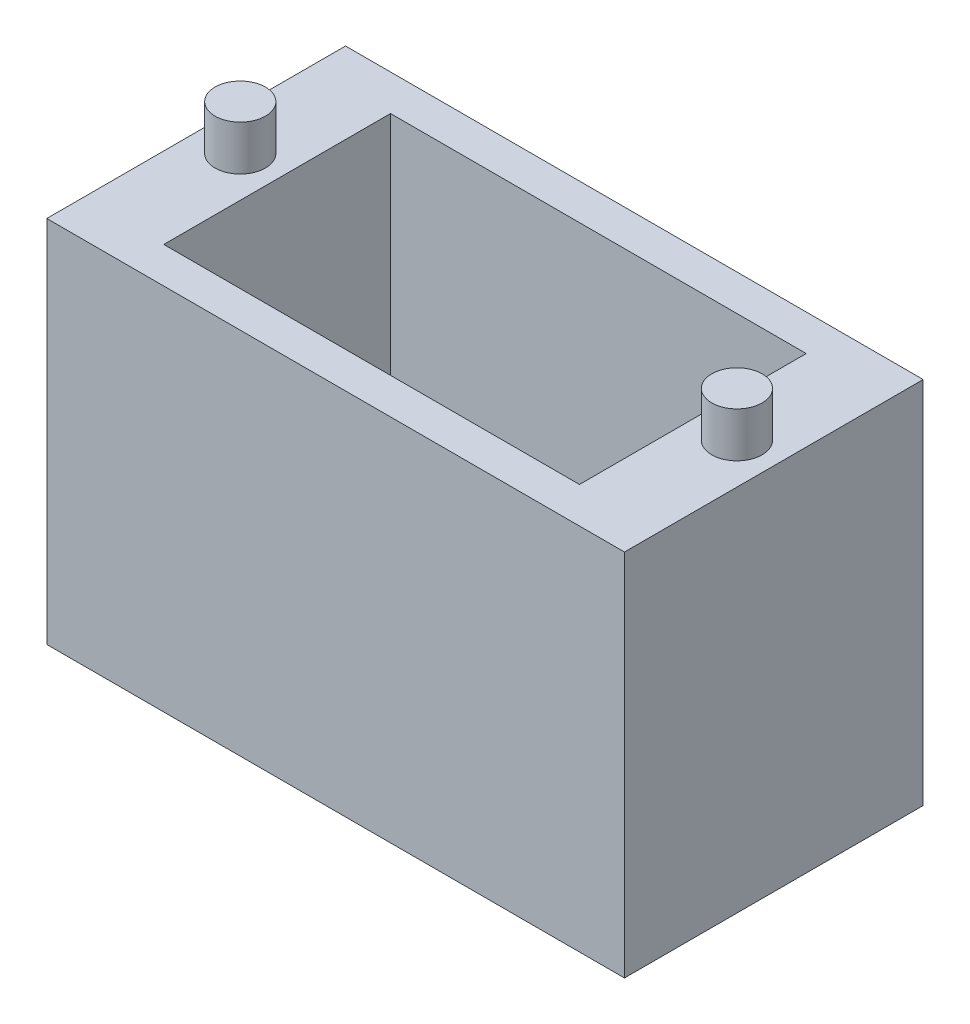
SolidWorks part; units mm, degrees
ref_plane "前视基准面" through (0, 0, 0) normal (0, 0, 1) x (1, 0, 0)
ref_plane "上视基准面" through (0, 0, 0) normal (0, 1, 0) x (1, 0, 0)
ref_plane "右视基准面" through (0, 0, 0) normal (1, 0, 0) x (0, 0, -1)
sketch "草图4" plane through (0, 0, 0) normal (0, 0, 1) x (1, 0, 0)
  line L0 (-11.55, 0) -> (11.55, 0)
  line L1 (11.55, 0) -> (11.55, 17)
  line L2 (16.05, -4.5) -> (16.05, 17)
  line L3 (0, 0) -> (0, 28356.0318) construction
  line L4 (-16.05, -4.5) -> (16.05, -4.5)
  line L5 (-11.55, 0) -> (-11.55, 17)
  line L6 (-16.05, -4.5) -> (-16.05, 17)
  line L7 (11.55, 17) -> (16.05, 17)
  line L8 (-11.55, 17) -> (-16.05, 17)
  point P10 (0, 0)
  dimension "D1" = 23.1
  dimension "D2" = 17
  dimension "D3" = 4.5
extrude "凸台-拉伸2" add sketch "草图4" along normal blind 12.2
sketch "草图5" plane through (0, -4.5, 0) normal (0, -1, 0) x (1, 0, 0)
  line L0 (-11.55, 12.2) -> (-11.55, 0) construction
  line L9 (-16.05, 0) -> (16.05, 0) construction
  line L10 (-11.55, 8.5) -> (-8.55, 8.5)
  line L11 (-11.55, 8.5) -> (-11.55, 0)
  line L12 (-11.55, 0) -> (-8.55, 0)
  line L13 (-8.55, 8.5) -> (-8.55, 0)
  point P94 (-10.8, 3.05)
  dimension "D1" = 3
  dimension "D2" = 8.5
extrude "切除-拉伸1" cut sketch "草图5" against normal through all
ref_plane "基准面4" through (0, 17, 0) normal (0, 1, 0) x (1, 0, 0)
sketch "草图6" plane through (0, 17, 0) normal (0, 1, 0) x (1, 0, 0)
  line L0 (11.55, 0) -> (16.05, -12.2) construction
  line L1 (16.05, 0) -> (11.55, -12.2) construction
  line L2 (11.55, -12.2) -> (-11.55, -12.2) construction
  line L3 (0, -12.2) -> (0, 0) construction
  circle A0 centre (13.8, -6.1) radius 1.4
  circle A1 centre (-13.8, -6.1) radius 1.4
  dimension "D1" = 2.8
extrude "凸台-拉伸3" add sketch "草图6" along normal blind 2.5
sketch "草图7" plane through (16.05, 0, 0) normal (1, 0, 0) x (0, 0, -1)
  line L0 (0, -4.5) -> (0, 17) construction
  line L1 (-12.2, -4.5) -> (0, -4.5)
  line L2 (-12.2, -4.5) -> (-12.2, -3.5)
  line L3 (-12.2, -3.5) -> (0, -3.5)
  line L4 (0, -4.5) -> (0, -3.5)
  line L5 (-6.1, -3.5) -> (-6.1, -4.5) construction
  line L6 (-12.2, -4) -> (0, -4) construction
  point P96 (-6.1, -4)
  dimension "D1" = 1
extrude "切除-拉伸2" cut sketch "草图7" against normal up to surface (32.1 mm away) and the other way through all up to face at (-16.05, 6.25, 6.1)
sketch "草图8" plane through (0, 0, 12.2) normal (0, 0, 1) x (1, 0, 0)
  line L0 (-11.55, 17) -> (-16.05, 17) construction
  line L1 (-16.05, 17) -> (-16.05, -3.5) construction
  line L2 (-16.05, -3.5) -> (16.05, -3.5) construction
  line L3 (16.05, 17) -> (11.55, 17) construction
  line L4 (16.05, -3.5) -> (16.05, 17) construction
  line L5 (11.55, 17) -> (11.55, 0) construction
  line L6 (11.55, 0) -> (-11.55, 0) construction
  line L7 (-11.55, 17) -> (-16.05, 17)
  line L8 (-16.05, 17) -> (-16.05, -3.5)
  line L9 (-16.05, -3.5) -> (16.05, -3.5)
  line L10 (16.05, 17) -> (11.55, 17)
  line L11 (16.05, -3.5) -> (16.05, 17)
  line L12 (11.55, 17) -> (11.55, 0)
  line L13 (11.55, 0) -> (-11.55, 0)
  line L14 (-11.55, 0) -> (-11.55, 17) construction
  line L15 (-11.55, 0) -> (-11.55, 17)
extrude "凸台-拉伸4" add sketch "草图8" along normal blind 0.2
sketch "草图9" plane through (0, 0, 12.4) normal (0, 0, 1) x (1, 0, 0)
  line L8 (-11.55, 0) -> (-11.55, 17)
  line L9 (-11.55, 17) -> (-16.05, 17)
  line L10 (-16.05, 17) -> (-16.05, -3.5)
  line L11 (-16.05, -3.5) -> (16.05, -3.5)
  line L12 (16.05, -3.5) -> (16.05, 17)
  line L13 (16.05, 17) -> (11.55, 17)
  line L14 (11.55, 17) -> (11.55, 0)
  line L15 (11.55, 0) -> (-11.55, 0)
  line L16 (-11.55, 0) -> (-11.55, 17)
  line L17 (-11.55, 17) -> (-16.05, 17)
  line L18 (-16.05, 17) -> (-16.05, -3.5)
  line L19 (-16.05, -3.5) -> (16.05, -3.5)
  line L20 (16.05, -3.5) -> (16.05, 17)
  line L21 (16.05, 17) -> (11.55, 17)
  line L22 (11.55, 17) -> (11.55, 0)
  line L23 (11.55, 0) -> (-11.55, 0)
  dimension "D1" = 0
extrude "凸台-拉伸5" add sketch "草图9" along normal blind 0.2
sketch "草图10" plane through (0, 0, 12.6) normal (0, 0, 1) x (1, 0, 0)
  line L1 (-16.05, 17) -> (16.05, 17)
  line L2 (-16.05, 17) -> (-16.05, -3.5)
  line L3 (-16.05, -3.5) -> (16.05, -3.5)
  line L4 (16.05, 17) -> (16.05, -3.5)
  line L5 (0, -3.5) -> (0, 17) construction
  line L6 (-16.05, 6.75) -> (16.05, 6.75) construction
  point P80 (0, 6.75)
extrude "凸台-拉伸6" add sketch "草图10" along normal blind 2
sketch "草图11" plane through (0, 0, 0) normal (0, 0, -1) x (-1, 0, 0)
  line L1 (-16.05, 17) -> (16.05, 17)
  line L2 (-16.05, 17) -> (-16.05, -3.5)
  line L3 (-16.05, -3.5) -> (16.05, -3.5)
  line L4 (16.05, 17) -> (16.05, -3.5)
  line L5 (0, -3.5) -> (0, 17) construction
  line L6 (-16.05, 6.75) -> (16.05, 6.75) construction
  point P84 (0, 6.75)
extrude "凸台-拉伸7" add sketch "草图11" along normal blind 2
